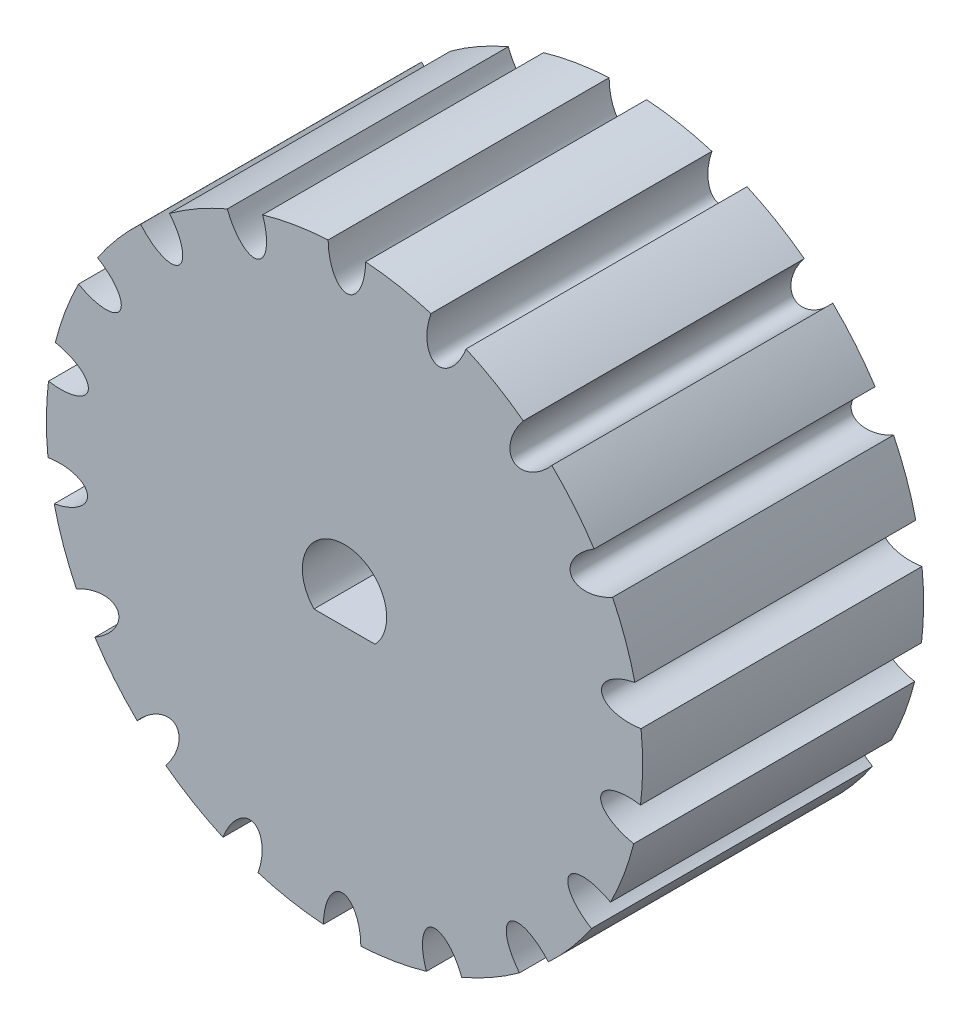
SolidWorks part; units mm, degrees
ref_plane "Front" through (0, 0, 0) normal (0, 0, 1) x (1, 0, 0)
ref_plane "Top" through (0, 0, 0) normal (0, 1, 0) x (1, 0, 0)
ref_plane "Right" through (0, 0, 0) normal (1, 0, 0) x (0, 0, -1)
sketch "Эскиз1" plane through (0, 0, 0) normal (0, 0, 1) x (1, 0, 0)
  circle A0 centre (0, 0) radius 15.9155
  dimension "D1" = 31.831
extrude "Бобышка-Вытянуть1" add sketch "Эскиз1" along normal blind 15
sketch "Эскиз2" plane through (0, 0, 15) normal (0, 0, 1) x (1, 0, 0)
  line L0 (1.631, -1.55) -> (-1.631, -1.55)
  arc A0 (1.631, -1.55) -> (-1.631, -1.55) centre (0, 0) ccw
  dimension "D1" = 4.5
  dimension "D2" = 1.55
extrude "Вырез-Вытянуть1" cut sketch "Эскиз2" against normal blind 15
sketch "Эскиз3" plane through (0, 0, 15) normal (0, 0, 1) x (1, 0, 0)
  circle A0 centre (0, 0) radius 15.9155 construction
  ellipse E0 centre (0.1258, 15.915) end of major axis (0.1258, 17.915) minor radius 1
  dimension "D1" = 2
  dimension "D2" = 4
extrude "Вырез-Вытянуть2" cut sketch "Эскиз3" against normal blind 15
pattern_circular "Круговой массив1" count 18 over 360 about axis through (0, 0, 15) along (0, 0, 1) of "Вырез-Вытянуть2"
